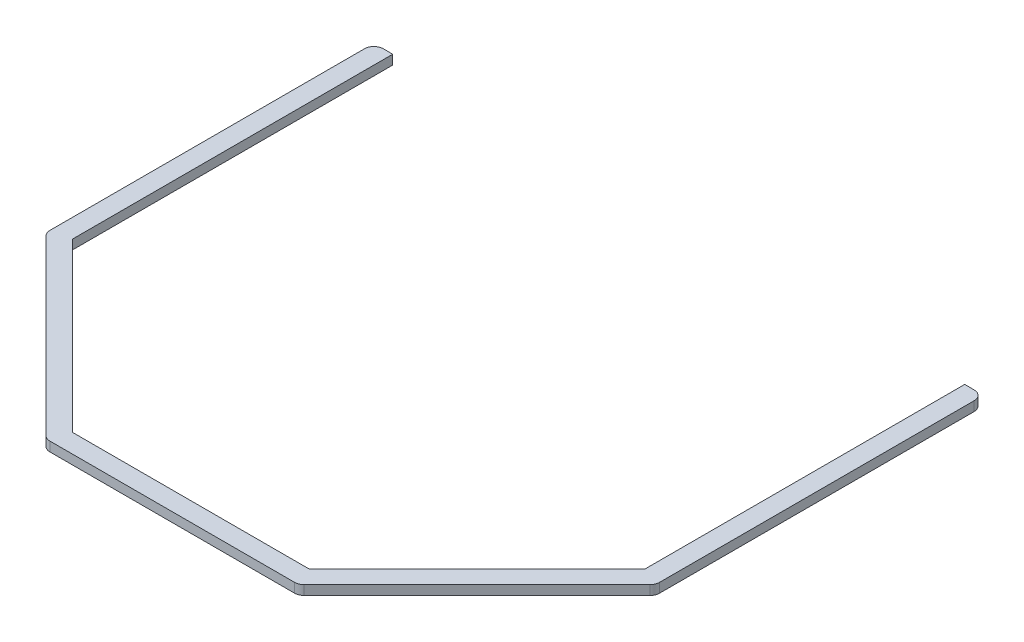
SolidWorks part; units mm, degrees
ref_plane "Front" through (0, 0, 0) normal (0, 0, 1) x (1, 0, 0)
ref_plane "Top" through (0, 0, 0) normal (0, 1, 0) x (1, 0, 0)
ref_plane "Right" through (0, 0, 0) normal (1, 0, 0) x (0, 0, -1)
sketch "Sketch1" plane through (0, 0, 0) normal (0, 1, 0) x (1, 0, 0)
  line L0 (-204.949, -85.5555) -> (-85.5555, -204.949) construction
  line L1 (-192.7177, 135.8868) -> (-192.7177, -79.8263)
  line L2 (-192.7177, -79.8263) -> (-79.8263, -192.7177)
  line L3 (-79.8263, -192.7177) -> (79.8263, -192.7177)
  line L4 (79.8263, -192.7177) -> (192.7177, -79.8263)
  line L5 (192.7177, -79.8263) -> (192.7177, 135.8868)
  line L7 (192.7177, 135.8868) -> (199.0677, 135.8868)
  line L9 (-205.4177, 85.0868) -> (-205.4177, -82.4565)
  line L10 (-203.5578, -86.9467) -> (-86.9467, -203.5578)
  line L11 (-82.4565, -205.4177) -> (82.4565, -205.4177)
  line L12 (86.9467, -203.5578) -> (203.5578, -86.9467)
  line L13 (205.4177, -82.4565) -> (205.4177, 85.0868)
  line L14 (205.4177, 85.0868) -> (85.0868, 205.4177) construction
  line L15 (85.0868, 205.4177) -> (-85.0868, 205.4177) construction
  line L16 (-85.0868, 205.4177) -> (-205.4177, 85.0868) construction
  line L17 (-205.4177, 85.0868) -> (-205.4177, 129.5368)
  line L18 (-199.0677, 135.8868) -> (-192.7177, 135.8868)
  line L19 (205.4177, 129.5368) -> (205.4177, 85.0868)
  line L20 (-136.272, 136.272) -> (-206.7612, 65.7828) [skipped]
  line L21 (0, 192.7177) -> (-99.6868, 192.7177) [skipped]
  line L22 (136.272, 136.272) -> (65.7828, 206.7612) [skipped]
  circle A0 centre (0, 0) radius 192.7177 construction
  circle A1 centre (0, 0) radius 205.4177 construction
  arc A2 (-205.4177, 129.5368) -> (-199.0677, 135.8868) centre (-199.0677, 129.5368) cw
  arc A3 (203.5578, -86.9467) -> (205.4177, -82.4565) centre (199.0677, -82.4565) ccw
  arc A4 (82.4565, -205.4177) -> (86.9467, -203.5578) centre (82.4565, -199.0677) ccw
  arc A5 (-86.9467, -203.5578) -> (-82.4565, -205.4177) centre (-82.4565, -199.0677) ccw
  arc A6 (-205.4177, -82.4565) -> (-203.5578, -86.9467) centre (-199.0677, -82.4565) ccw
  arc A7 (199.0677, 135.8868) -> (205.4177, 129.5368) centre (199.0677, 129.5368) cw
  dimension "D1" = 6.35
  dimension "D4" = 6.35
  dimension "D2" = 12.7
  dimension "D3" = 50.8
extrude "Boss-Extrude1" add sketch "Sketch1" along normal blind 6.35
